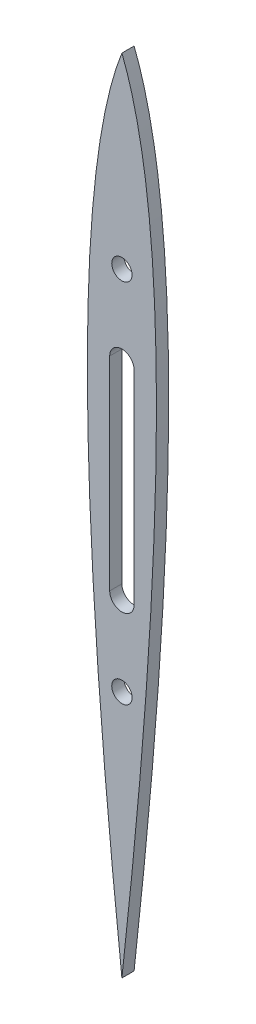
SolidWorks part; units mm, degrees
ref_plane "Front Plane" through (0, 0, 0) normal (0, 0, 1) x (1, 0, 0)
ref_plane "Top Plane" through (0, 0, 0) normal (0, 1, 0) x (1, 0, 0)
ref_plane "Right Plane" through (0, 0, 0) normal (1, 0, 0) x (0, 0, -1)
sketch "Sketch1" plane through (0, 0, 0) normal (0, 0, 1) x (1, 0, 0)
  line L0 (-2.2678, 148.3484) -> (-30.5724, 92.2411) construction
  line L1 (-30.5724, 92.2411) -> (0, -152.4) construction
  line L2 (0, 57.15) -> (0, -6.35) construction
  line L6 (2.2678, 148.3484) -> (30.5724, 92.2411) construction
  line L7 (30.5724, 92.2411) -> (0, -152.4) construction
  line L8 (3.81, 57.15) -> (3.81, -6.35)
  line L9 (-3.81, 57.15) -> (-3.81, -6.35)
  arc A0 (-2.2678, 148.3484) -> (2.2678, 148.3484) centre (0, 147.2043) cw construction
  arc A1 (0, 140.978) -> (0, 140.978) centre (0, 140.978) cw
  circle A2 centre (0, 82.55) radius 3.175
  circle A3 centre (0, -31.75) radius 3.175
  arc A4 (3.81, 57.15) -> (-3.81, 57.15) centre (0, 57.15) ccw
  arc A5 (-3.81, -6.35) -> (3.81, -6.35) centre (0, -6.35) ccw
  spline S0 degree 2 poles (-2.2678, 148.3484) (-30.5724, 92.2411) (0, -152.4) knots 0 0 0 1 1 1 construction
  spline S1 degree 2 poles (2.2678, 148.3484) (30.5724, 92.2411) (0, -152.4) knots 0 0 0 1 1 1 construction
  spline S2 degree 1 poles (0, 140.978) (0, -109.1253) knots 0 0 1 1 construction
  spline S3 degree 1 poles (0, 140.978) (0, -109.1253) knots 0 0 1 1 construction
  spline S4 degree 2 poles (0, 140.978) (3.9185, 131.1561) (8.1694, 106.0556) (10.2426, 81.4333) (11.1457, 45.0402) (8.1637, -35.5088) (0, -109.1253) knots 0.045527 0.045527 0.045527 0.207531 0.315533 0.423536 0.585539 0.909547 0.909547 0.909547
  spline S5 degree 2 poles (0, -109.1253) (-8.1637, -35.5088) (-11.1457, 45.0402) (-10.2426, 81.4333) (-8.1694, 106.0556) (-3.9185, 131.1561) (0, 140.978) knots 0.045527 0.045527 0.045527 0.369534 0.531538 0.639541 0.747543 0.909547 0.909547 0.909547
  point P8 (0, 25.4)
  dimension "D1" = 2.54
  dimension "D3" = 6.35
  dimension "D7" = 31.75
  dimension "D8" = 3.81
  dimension "D4" = 114.3
  dimension "D5" = 63.5
  dimension "D6" = 57.15
  dimension "D2" = 5.08
extrude "Main extrude" add sketch "Sketch1" along normal blind 3.81
